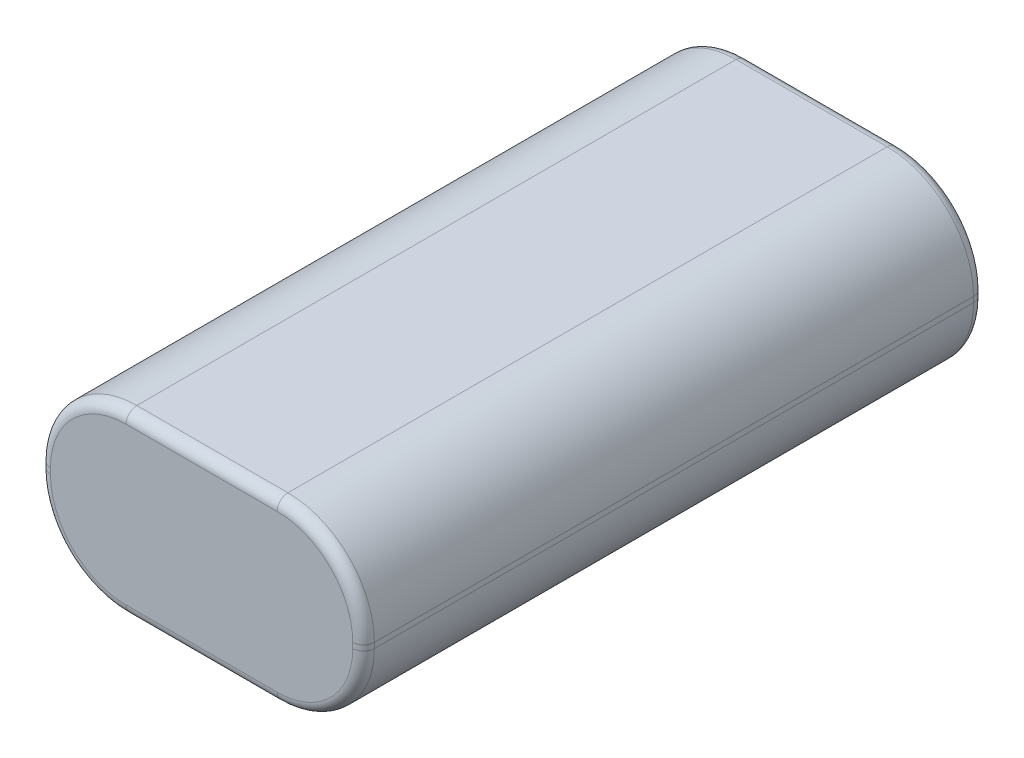
SolidWorks part; units mm, degrees
ref_plane "Front Plane" through (0, 0, 0) normal (0, 0, 1) x (1, 0, 0)
ref_plane "Top Plane" through (0, 0, 0) normal (0, 1, 0) x (1, 0, 0)
ref_plane "Right Plane" through (0, 0, 0) normal (1, 0, 0) x (0, 0, -1)
sketch "Sketch1" plane through (0, 0, 0) normal (0, 0, 1) x (1, 0, 0)
  line L1 (8, 0) -> (22, 0)
  line L2 (0, 8) -> (0, 8.5)
  line L3 (8, 16.5) -> (22, 16.5)
  line L4 (30, 8) -> (30, 8.5)
  arc A0 (0, 8) -> (8, 0) centre (8, 8) ccw
  arc A1 (22, 0) -> (30, 8) centre (22, 8) ccw
  arc A2 (30, 8.5) -> (22, 16.5) centre (22, 8.5) ccw
  arc A3 (8, 16.5) -> (0, 8.5) centre (8, 8.5) ccw
  point P7 (0, 0)
  point P12 (30, 16.5)
  point P15 (0, 16.5)
  dimension "D3" = 8
  dimension "D1" = 30
  dimension "D2" = 16.5
extrude "Boss-Extrude1" add sketch "Sketch1" along normal blind 57.5
fillet "Fillet1" radius 1 16 edges at (15, 0, 0) (27.6569, 2.3431, 0) (30, 8.25, 0) (27.6569, 14.1569, 0) (15, 16.5, 0) (2.3431, 14.1569, 0) (0, 8.25, 0) (2.3431, 2.3431, 0) (0, 8.25, 57.5) (2.3431, 14.1569, 57.5) (15, 16.5, 57.5) (27.6569, 14.1569, 57.5) (30, 8.25, 57.5) (27.6569, 2.3431, 57.5) (15, 0, 57.5) (2.3431, 2.3431, 57.5)
